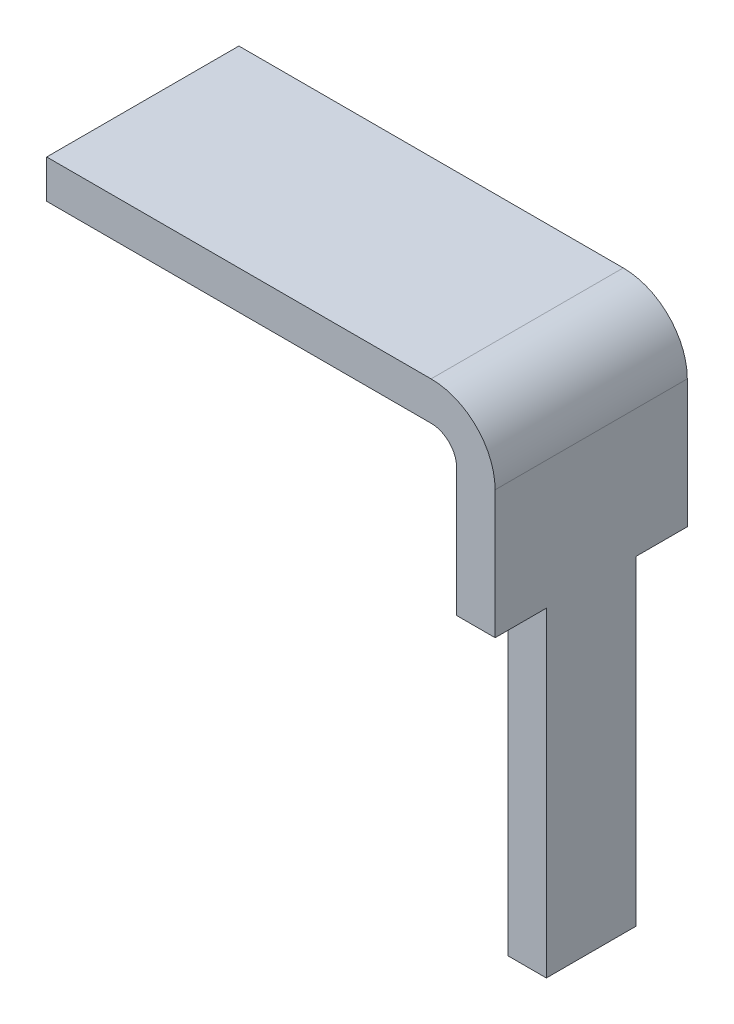
SolidWorks part; units mm, degrees
ref_plane "Front Plane" through (0, 0, 0) normal (0, 0, 1) x (1, 0, 0)
ref_plane "Top Plane" through (0, 0, 0) normal (0, 1, 0) x (1, 0, 0)
ref_plane "Right Plane" through (0, 0, 0) normal (1, 0, 0) x (0, 0, -1)
sketch "Sketch1" plane through (0, 0, 0) normal (0, 0, 1) x (1, 0, 0)
  line L0 (0, 0) -> (3, 0)
  line L1 (3.5, -0.5) -> (3.5, -4)
  line L2 (0, -0.3) -> (3, -0.3)
  line L3 (3.2, -0.5) -> (3.2, -4)
  line L4 (0, 0) -> (0, -0.3)
  line L5 (3.2, -4) -> (3.5, -4)
  arc A0 (3, 0) -> (3.5, -0.5) centre (3, -0.5) cw
  arc A1 (3, -0.3) -> (3.2, -0.5) centre (3, -0.5) cw
  dimension "D1" = 0.5
  dimension "D3" = 4
  dimension "D4" = 3
  dimension "D2" = 0.3
extrude "Boss-Extrude1" add sketch "Sketch1" along normal blind 1.5
sketch "Sketch2" plane through (3.5, 0, 0) normal (1, 0, 0) x (0, 0, -1)
  line L0 (-1.5, -4) -> (-1.5, -0.5) construction
  line L1 (-1.5, -1.5) -> (-1.1, -1.5)
  line L2 (-1.5, -1.5) -> (-1.5, -4)
  line L3 (-1.5, -4) -> (-1.1, -4)
  line L4 (-1.1, -1.5) -> (-1.1, -4)
  line L5 (-1.5, -4) -> (0, -4) construction
  line L6 (-0.75, -4) -> (-0.75, -1.807) construction
  line L7 (0, -4) -> (-0.4, -4)
  line L8 (-0.4, -1.5) -> (-0.4, -4)
  line L9 (0, -1.5) -> (-0.4, -1.5)
  line L10 (0, -1.5) -> (0, -4)
  point P8 (-0.75, -4)
  dimension "D1" = 2.5
  dimension "D2" = 0.35
extrude "Cut-Extrude1" cut sketch "Sketch2" against normal blind 1.5
